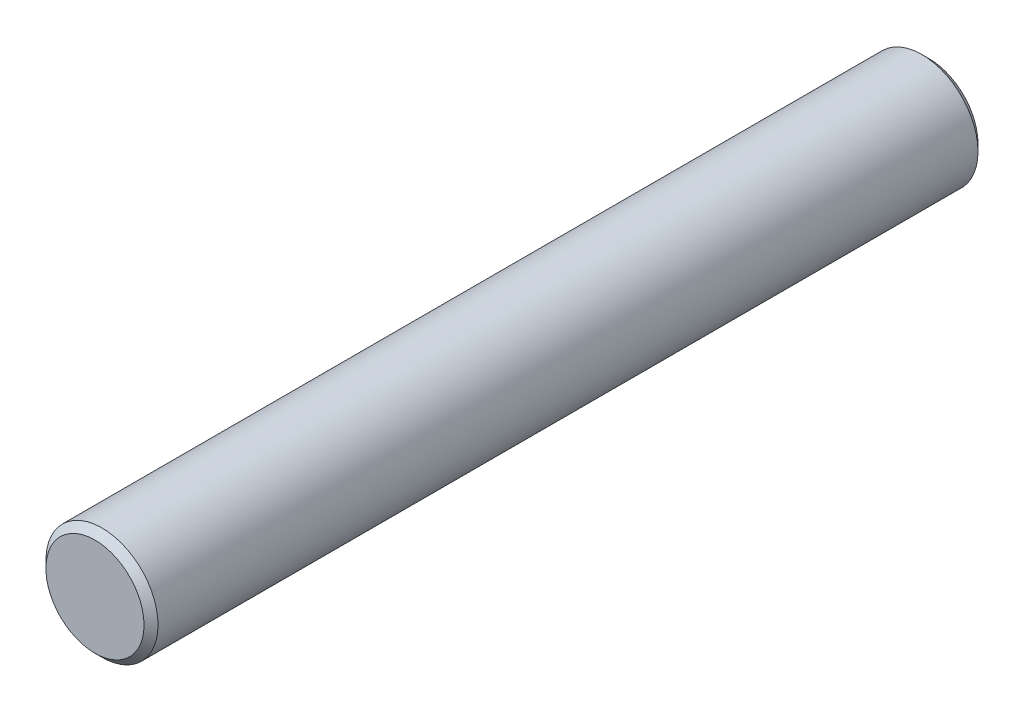
SolidWorks part; units mm, degrees
ref_plane "Front Plane" through (0, 0, 0) normal (0, 0, 1) x (1, 0, 0)
ref_plane "Top Plane" through (0, 0, 0) normal (0, 1, 0) x (1, 0, 0)
ref_plane "Right Plane" through (0, 0, 0) normal (1, 0, 0) x (0, 0, -1)
sketch "Sketch2" plane through (0, 0, 0) normal (0, 0, 1) x (1, 0, 0)
  circle A0 centre (0, 0) radius 8
  dimension "D1" = 16
extrude "Boss-Extrude1" add sketch "Sketch2" along normal mid plane 119
chamfer "Chamfer1" distance 1 angle 45 2 edges at (8, 0, -59.5) (8, 0, 59.5)
